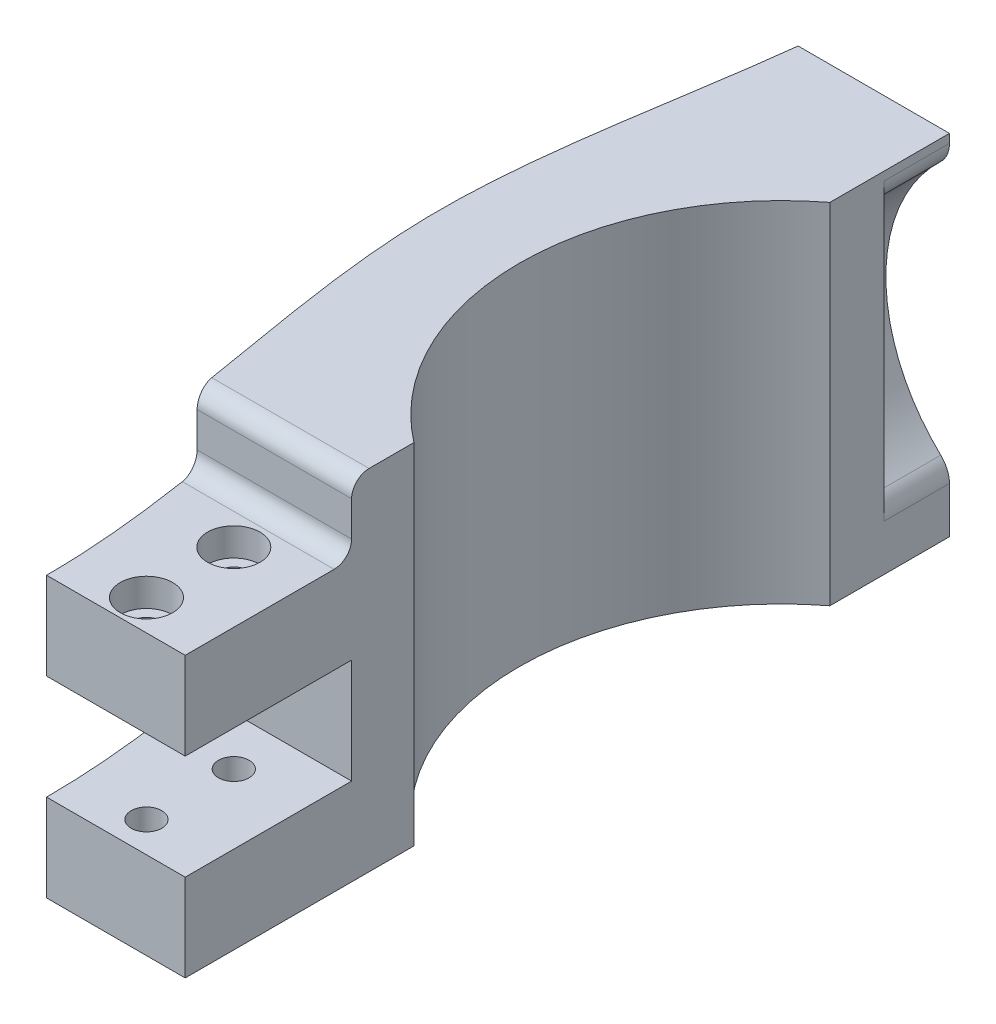
SolidWorks part; units mm, degrees
ref_plane "Front Plane" through (0, 0, 0) normal (0, 0, 1) x (1, 0, 0)
ref_plane "Top Plane" through (0, 0, 0) normal (0, 1, 0) x (1, 0, 0)
ref_plane "Right Plane" through (0, 0, 0) normal (1, 0, 0) x (0, 0, -1)
sketch "Sketch1" plane through (0, 0, 0) normal (0, 1, 0) x (1, 0, 0)
  line L0 (0, -50) -> (0, 50)
  line L1 (50, -50) -> (-50, -50)
  line L2 (50, -50) -> (50, 50)
  line L3 (50, 50) -> (-50, 50)
  line L4 (-50, -50) -> (-50, 50)
  line L5 (50, -50) -> (-50, 50) construction
  line L6 (50, 50) -> (-50, -50) construction
  circle A0 centre (0, 0) radius 30
  point P10 (0, 0)
  dimension "D1" = 60
  dimension "D2" = 100
extrude "Boss-Extrude1" add sketch "Sketch1" along normal blind 40 contours A0 L0 L3 L4 L1 | A0 L0 L1 L2 L3
sketch "Sketch2" plane through (0, 0, -50) normal (0, 0, -1) x (-1, 0, 0)
  line L0 (-50, 20) -> (50, 20) construction
  line L1 (0, 34.1421) -> (-14.1421, 20)
  line L2 (-14.1421, 20) -> (0, 5.8579)
  line L3 (0, 5.8579) -> (14.1421, 20)
  line L4 (14.1421, 20) -> (0, 34.1421)
  line L5 (-50, 40) -> (-50, 0) construction
  line L6 (50, 40) -> (50, 0) construction
  circle A0 centre (0, 20) radius 10 construction
  dimension "D1" = 20
extrude "Cut-Extrude1" [suppressed] cut sketch "Sketch2" against normal up to next
sketch "Sketch3" plane through (0, 0, 50) normal (0, 0, 1) x (1, 0, 0)
  line L0 (-50, 20) -> (50, 20) construction
  line L1 (-30.95, 40) -> (-18.25, 40)
  line L2 (-30.95, 40) -> (-30.95, 0)
  line L3 (-30.95, 0) -> (-18.25, 0)
  line L4 (-18.25, 40) -> (-18.25, 0)
  line L5 (-50, 40) -> (-50, 0) construction
  line L6 (50, 40) -> (50, 0) construction
  line L7 (-24.6, 40) -> (-24.6, 0) construction
  line L8 (50, 40) -> (-50, 40) construction
  point P10 (-30.95, 20)
  dimension "D1" = 12.7
  dimension "D2" = 25.4
extrude "Boss-Extrude2" add sketch "Sketch3" along normal blind 27.178
sketch "Sketch4" plane through (0, 0, 0) normal (1, 0, 0) x (0, 0, -1)
  line L1 (-92.4894, -65.8669) -> (92.4894, -65.8669)
  line L2 (-92.4894, -65.8669) -> (-92.4894, 65.8669)
  line L3 (-92.4894, 65.8669) -> (92.4894, 65.8669)
  line L4 (92.4894, -65.8669) -> (92.4894, 65.8669)
  line L5 (-92.4894, -65.8669) -> (92.4894, 65.8669) construction
  line L6 (-92.4894, 65.8669) -> (92.4894, -65.8669) construction
extrude "Cut-Extrude2" cut sketch "Sketch4" along normal through all
sketch "Sketch5" plane through (0, 0, 0) normal (1, 0, 0) x (0, 0, -1)
  line L1 (72.0832, -70.0065) -> (-72.0832, -70.0065)
  line L2 (72.0832, -70.0065) -> (72.0832, 70.0065)
  line L3 (72.0832, 70.0065) -> (-72.0832, 70.0065)
  line L4 (-72.0832, -70.0065) -> (-72.0832, 70.0065)
  line L5 (72.0832, -70.0065) -> (-72.0832, 70.0065) construction
  line L6 (72.0832, 70.0065) -> (-72.0832, -70.0065) construction
extrude "Cut-Extrude3" cut sketch "Sketch5" against normal up to surface (18.25 mm away) up to face at (-18.25, 20, 63.589)
sketch "Sketch6" plane through (0, 0, -50) normal (0, 0, -1) x (-1, 0, 0)
  line L0 (18.25, 40) -> (18.25, 0) construction
  line L2 (28.8566, 20) -> (18.25, 30.6066) construction
  line L3 (18.25, 30.6066) -> (7.6434, 20) construction
  line L4 (7.6434, 20) -> (18.25, 9.3934) construction
  line L5 (18.25, 9.3934) -> (28.8566, 20) construction
  circle A0 centre (18.25, 20) radius 7.5 construction
  circle A1 centre (18.25, 20) radius 20 construction
  circle A2 centre (5.5297, 22.15) radius 20
  point P11 (0, 0)
  point P12 (5.2637, 20)
  point P13 (0, 0)
  point P14 (5.2403, 23.072)
  point P16 (5.5297, 22.15)
  dimension "D1" = 15
  dimension "D2" = 40
  dimension "D3" = 40
extrude "Cut-Extrude4" cut sketch "Sketch6" against normal blind 20
fillet "Fillet3" [suppressed] radius 6.35
fillet "Fillet4" radius 3.175 2 edges at (-18.25, 6.7164, -40) (-18.25, 37.5835, -40)
sketch "Sketch7" plane through (0, 0, 77.178) normal (0, 0, 1) x (1, 0, 0)
  line L1 (-48.3261, -46.7932) -> (48.3261, -46.7932)
  line L2 (-48.3261, -46.7932) -> (-48.3261, 46.7932)
  line L3 (-48.3261, 46.7932) -> (48.3261, 46.7932)
  line L4 (48.3261, -46.7932) -> (48.3261, 46.7932)
  line L5 (-48.3261, -46.7932) -> (48.3261, 46.7932) construction
  line L6 (-48.3261, 46.7932) -> (48.3261, -46.7932) construction
  point P0 (0, 0)
extrude "Cut-Extrude5" cut sketch "Sketch7" against normal up to surface (27.178 mm away) up to face at (-40.475, 20, 50)
sketch "Sketch8" plane through (0, 40, 0) normal (0, 1, 0) x (1, 0, 0)
  line L0 (-18.25, -50) -> (-50, -50) construction
  line L1 (-34.76, 50) -> (-50, 50)
  line L2 (-18.25, 50) -> (-50, 50) construction
  line L3 (-50, -50) -> (-50, 50) construction
  line L4 (-50, -50) -> (-50, 50)
  line L5 (-34.125, -50) -> (-50, -50)
  spline S0 degree 3 poles (-34.125, -50) (-34.125, -33.2412) (-45.237, -0.0937) (-34.76, 33.3302) (-34.76, 50) knots 0 0 0 0 0.50037 1 1 1 1
  point P16 (-50, 0)
  dimension "D1" = 10.16
  dimension "D2" = 15.24
extrude "Cut-Extrude6" cut sketch "Sketch8" against normal through all
sketch "Sketch9" plane through (0, 40, 0) normal (0, 1, 0) x (1, 0, 0)
  line L0 (-18.25, -30.95) -> (-35.933, -30.95)
  line L1 (-18.25, -50) -> (-18.25, -23.8104) construction
  line L2 (-18.25, -30.95) -> (-18.25, -50)
  line L3 (-18.25, -50) -> (-34.125, -50)
  spline S0 degree 3 poles (-2004.9014, -357.9043) (168.4568, -203.1879) (-248.5847, -1.5) (169.3358, 210.8777) (-2014.0992, 296.1428) knots -2.59149 -2.59149 -2.59149 -2.59149 0.50037 3.62745 3.62745 3.62745 3.62745 only from (-34.125, -50) to (-34.76, 50) construction
  spline S1 degree 3 poles (-34.125, -50) (-34.125, -33.2412) (-45.237, -0.0937) (-34.76, 33.3302) (-34.76, 50) knots 0 0 0 0 0.50037 1 1 1 1
  spline M3 degree 3 poles (-34.76, 50) (-34.76, 33.3302) (-45.237, -0.0937) (-34.125, -33.2412) (-34.125, -50) knots 0 0 0 0 0.49963 1 1 1 1
  line M4 (-34.125, -50) -> (-18.25, -50)
  line M5 (-18.25, -50) -> (-18.25, -23.8104)
  dimension "D1" = 19.05
extrude "Cut-Extrude7" cut sketch "Sketch9" against normal blind 8 contours L0 M5 M3 M4
ref_plane "Plane1" through (0, 16, 0) normal (0, 1, 0) x (1, 0, 0)
mirror "Mirror1" [suppressed] about plane through (0, 16, 0) normal (0, 1, 0)
fillet "Fillet5" radius 2 2 edges at (-27.0915, 32, 30.95) (-27.0915, 40, 30.95)
sketch "Sketch10" plane through (0, 32, 0) normal (0, 1, 0) x (1, 0, 0)
  line L0 (-26.1875, -50) -> (-26.1875, -32.95) construction
  line L1 (-34.125, -50) -> (-18.25, -50) construction
  line L2 (-18.25, -32.95) -> (-35.6232, -32.95) construction
  circle A0 centre (-26.1875, -46.5) radius 1.75
  circle A1 centre (-26.1875, -36.5) radius 1.75
  dimension "D1" = 3.5
  dimension "D4" = 3.5
  dimension "D2" = 10
  dimension "D3" = 3.5
extrude "Cut-Extrude8" cut sketch "Sketch10" against normal through all
sketch "Sketch11" plane through (0, 0, 50) normal (0, 0, 1) x (1, 0, 0)
  line L0 (-34.125, 16) -> (-18.25, 16) construction
  line L2 (-34.125, 10) -> (-18.25, 10)
  line L3 (-34.125, 10) -> (-34.125, 22)
  line L4 (-34.125, 32) -> (-34.125, 0)
  line L5 (-34.125, 0) -> (-18.25, 0)
  line L6 (-18.25, 0) -> (-18.25, 32)
  line L7 (-18.25, 32) -> (-34.125, 32)
  line L8 (-34.125, 32) -> (-34.125, 0) construction
  line L10 (-18.25, 0) -> (-18.25, 32) construction
  line L11 (-18.25, 32) -> (-34.125, 32) construction
  line L12 (-34.125, 22) -> (-18.25, 22)
  line L13 (-18.25, 10) -> (-18.25, 22)
  line L14 (-34.125, 10) -> (-18.25, 22) construction
  line L15 (-34.125, 22) -> (-18.25, 10) construction
  line L16 (-26.1875, 22) -> (-43.6768, 22)
  line L17 (-26.1875, 22) -> (-26.1875, 10)
  line L18 (-26.1875, 10) -> (-43.6768, 10)
  line L19 (-43.6768, 22) -> (-43.6768, 10)
  line L23 (-34.125, 0) -> (-18.25, 0)
  point P6 (-26.1875, 16)
  point P15 (0, 0)
  line M9 (-34.125, 32) -> (-34.125, 0)
  line M11 (-18.25, 0) -> (-18.25, 32)
  dimension "D2" = 12
  dimension "D1" = 0
extrude "Cut-Extrude9" cut sketch "Sketch11" against normal blind 19.05 contours L16 L19 L18 M9 | L17 L12 L2 M9 | L12 L17 L2 M11
sketch "Sketch14" plane through (0, 32, 0) normal (0, 1, 0) x (1, 0, 0)
  circle A0 centre (-26.1875, -36.5) radius 3
  circle A1 centre (-26.1875, -46.5) radius 3
  dimension "D1" = 6
  dimension "D2" = 6
extrude "Cut-Extrude10" cut sketch "Sketch14" against normal blind 3.2
mirror "Mirror2" about plane through (0, 16, 0) normal (0, 1, 0) of "Cut-Extrude10"
sketch "Sketch15" plane through (0, 0, -50) normal (0, 0, -1) x (-1, 0, 0)
  line L1 (0, 0) -> (61.0985, 0)
  line L2 (0, 0) -> (0, 49.7438)
  line L3 (0, 49.7438) -> (61.0985, 49.7438)
  line L4 (61.0985, 0) -> (61.0985, 49.7438)
extrude "Cut-Extrude11" cut sketch "Sketch15" against normal blind 12.5
